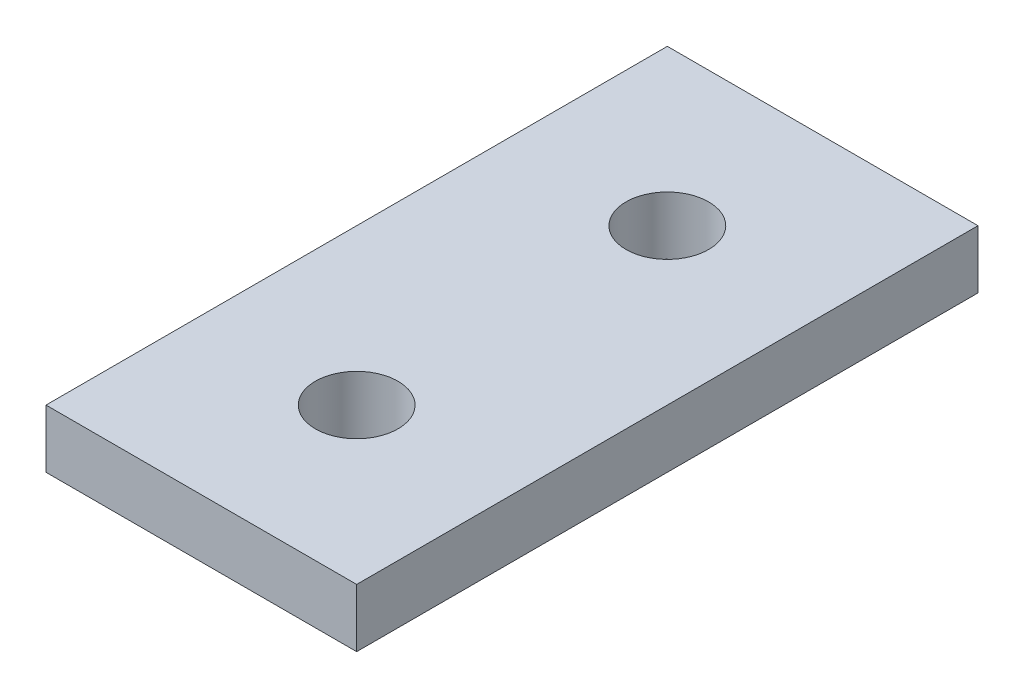
SolidWorks part; units mm, degrees
ref_plane "Front Plane" through (0, 0, 0) normal (0, 0, 1) x (1, 0, 0)
ref_plane "Top Plane" through (0, 0, 0) normal (0, 1, 0) x (1, 0, 0)
ref_plane "Right Plane" through (0, 0, 0) normal (1, 0, 0) x (0, 0, -1)
sketch "Sketch1" plane through (0, 0, 0) normal (0, 1, 0) x (1, 0, 0)
  line L0 (12.7, 50.8) -> (12.7, 38.1) construction
  line L1 (0, 0) -> (25.4, 0)
  line L2 (0, 0) -> (0, 50.8)
  line L3 (0, 50.8) -> (25.4, 50.8)
  line L4 (25.4, 0) -> (25.4, 50.8)
  line L5 (12.7, 38.1) -> (12.7, 12.7) construction
  line L6 (12.7, 12.7) -> (12.7, 0) construction
  circle A0 centre (12.7, 38.1) radius 3.3782
  circle A1 centre (12.7, 12.7) radius 3.3782
  dimension "D3" = 6.7564
  dimension "D1" = 25.4
  dimension "D2" = 50.8
  dimension "D4" = 12.7
extrude "Boss-Extrude1" add sketch "Sketch1" along normal blind 4.7625
